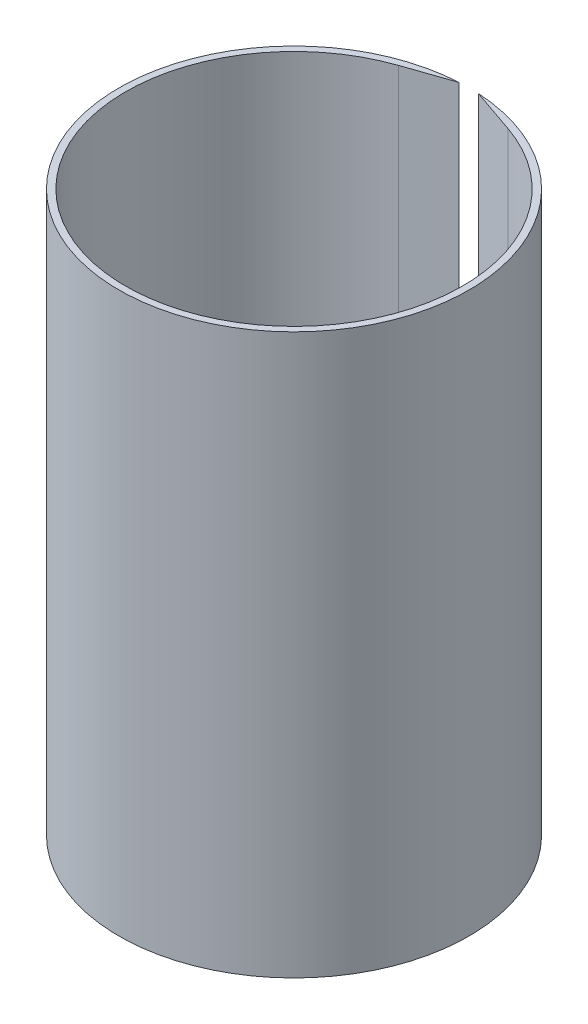
SolidWorks part; units mm, degrees
material "PTFE (general)"
ref_plane "Front Plane" through (0, 0, 0) normal (0, 0, 1) x (1, 0, 0)
ref_plane "Top Plane" through (0, 0, 0) normal (0, 1, 0) x (1, 0, 0)
ref_plane "Right Plane" through (0, 0, 0) normal (1, 0, 0) x (0, 0, -1)
sketch "Sketch1" plane through (0, 0, 0) normal (0, 1, 0) x (1, 0, 0)
  line L0 (0, 0) -> (0, 53.5853) construction
  line L1 (-2.286, 41.6568) -> (-13.0642, 37.9461)
  line L2 (2.286, 41.6568) -> (13.0237, 37.96)
  arc A0 (-13.0642, 37.9461) -> (13.0237, 37.96) centre (0, 0) ccw
  arc A1 (-2.286, 41.6568) -> (2.286, 41.6568) centre (0, 0) ccw
  point P3 (0, 0)
  point P6 (13.1164, 37.9639)
  point P9 (0, 0)
  point P10 (0, 0)
  point P11 (29.5452, 31.1453)
  point P12 (0, 0)
  point P13 (29.4181, 32.2892)
  point P14 (-13.0931, 37.956)
  dimension "D1" = 80.264
  dimension "D2" = 83.439
  dimension "D3" = 2.286
  dimension "D4" = 2.286
extrude "Boss-Extrude1" add sketch "Sketch1" along normal blind 133.35
